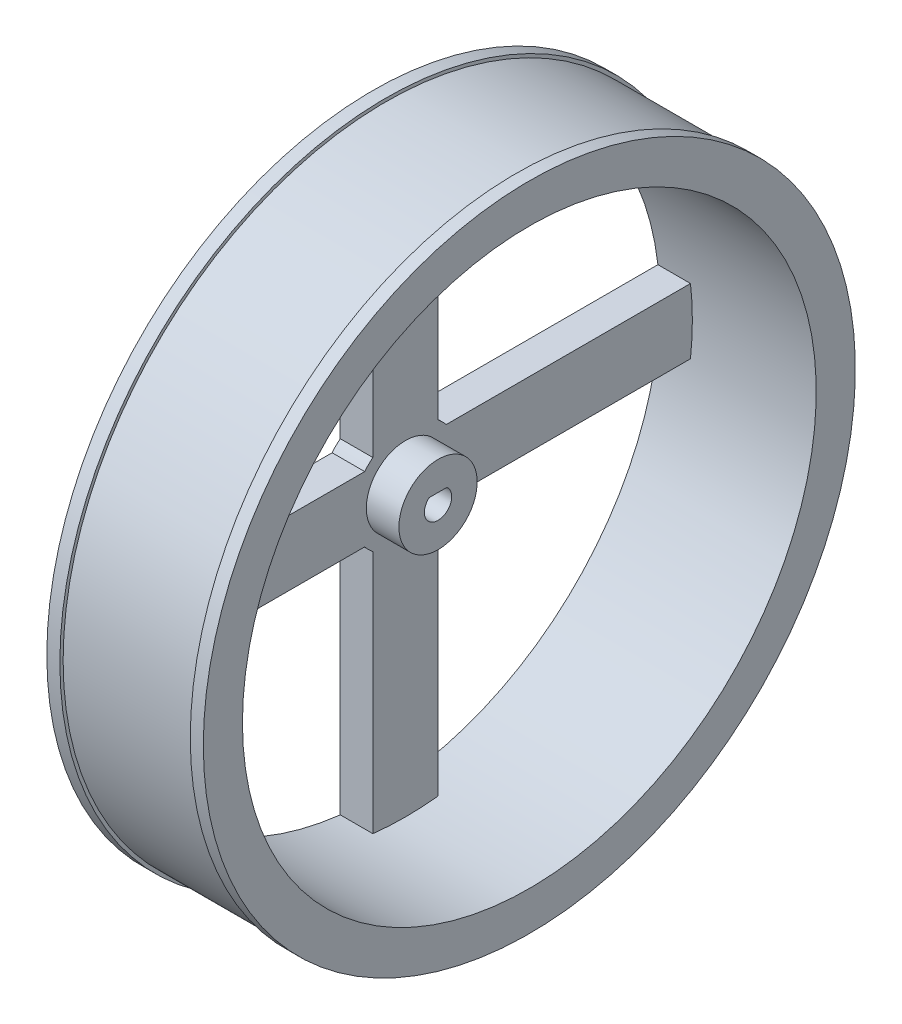
SolidWorks part; units mm, degrees
material "PLA (Black)"
ref_plane "Front Plane" through (0, 0, 0) normal (0, 0, 1) x (1, 0, 0)
ref_plane "Top Plane" through (0, 0, 0) normal (0, 1, 0) x (1, 0, 0)
ref_plane "Right Plane" through (0, 0, 0) normal (1, 0, 0) x (0, 0, -1)
sketch "Sketch1" plane through (0, 0, 0) normal (0, 0, 1) x (1, 0, 0)
  line L0 (0, 0) -> (41532.2986, 0) construction
  line L1 (-12, 50) -> (-12, 44)
  line L3 (12, 44) -> (12, 50)
  line L4 (12, 50) -> (10, 50)
  line L5 (10, 50) -> (10, 49.5)
  line L6 (10, 49.5) -> (-10, 49.5)
  line L7 (-10, 49.5) -> (-10, 50)
  line L8 (-10, 50) -> (-12, 50)
  line L9 (-12, 44) -> (12, 44)
  line L10 (-2, 6) -> (-12, 6)
  line L11 (-12, 6) -> (-12, 0)
  line L12 (-12, 0) -> (-2, 0)
  line L13 (-2, 0) -> (-2, 6)
  point P15 (0, 44)
  dimension "D1" = 100
  dimension "D2" = 0.5
  dimension "D3" = 2
  dimension "D4" = 20
  dimension "D5" = 6
  dimension "D6" = 12
  dimension "D7" = 10
revolve "Revolve1" add sketch "Sketch1" angle 360 about L0
sketch "Sketch2" plane through (-12, 0, 0) normal (1, 0, 0) x (0, 0, -1)
  line L2 (0, 0) -> (0, 50000) construction
  line L9 (-5, 6.245) -> (-5, 43.715)
  line L10 (5, 6.245) -> (5, 43.715)
  arc A0 (-5, 43.715) -> (5, 43.715) centre (0, 0) cw
  arc A11 (-5, 6.245) -> (5, 6.245) centre (0, 0) ccw
  circle A12 centre (0, 0) radius 44 construction
  circle A13 centre (0, 0) radius 6
  circle A14 centre (0, 0) radius 6
  dimension "D1" = 16
  dimension "D2" = 10
  dimension "D3" = 0
extrude "Boss-Extrude1" add sketch "Sketch2" along normal blind 5
sketch "Sketch3" plane through (-2, 0, 0) normal (1, 0, 0) x (0, 0, -1)
  line L0 (-1.3601, 1.6) -> (1.3601, 1.6)
  arc A0 (-1.3601, 1.6) -> (1.3601, 1.6) centre (0, 0) ccw
  dimension "D1" = 4.2
  dimension "D2" = 1.6
extrude "Cut-Extrude1" cut sketch "Sketch3" against normal through all both and the other way through all
pattern_circular "CirPattern1" count 4 over 360 about axis through (0, 0, 0) along (1, 0, 0) of "Boss-Extrude1"
